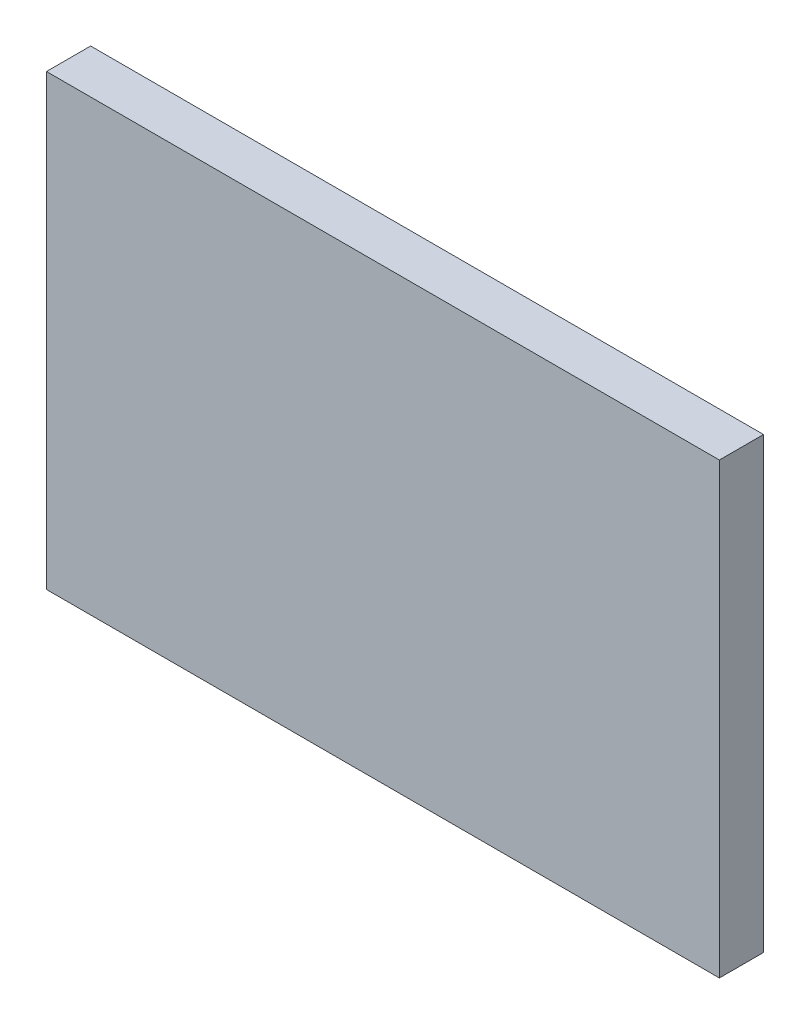
SolidWorks part; units mm, degrees
ref_plane "Front Plane" through (0, 0, 0) normal (0, 0, 1) x (1, 0, 0)
ref_plane "Top Plane" through (0, 0, 0) normal (0, 1, 0) x (1, 0, 0)
ref_plane "Right Plane" through (0, 0, 0) normal (1, 0, 0) x (0, 0, -1)
sketch "Sketch1" plane through (0, 0, 0) normal (0, 0, 1) x (1, 0, 0)
  line L0 (-7.62, 5.08) -> (7.62, 5.08)
  line L1 (7.62, 5.08) -> (7.62, -5.08)
  line L2 (7.62, -5.08) -> (-7.62, -5.08)
  line L3 (-7.62, -5.08) -> (-7.62, 5.08)
extrude "Component_Outline" add sketch "Sketch1" along normal blind 1 separate body
sketch3d "3DSketch1"
  line L0 (0, 0, 0) -> (1, 0, 0)
  line L1 (0, 0, 0) -> (0, 1, 0)
  line L2 (0, 0, 0) -> (0, 0, 1)
  point P0 (0, 0, 0)
